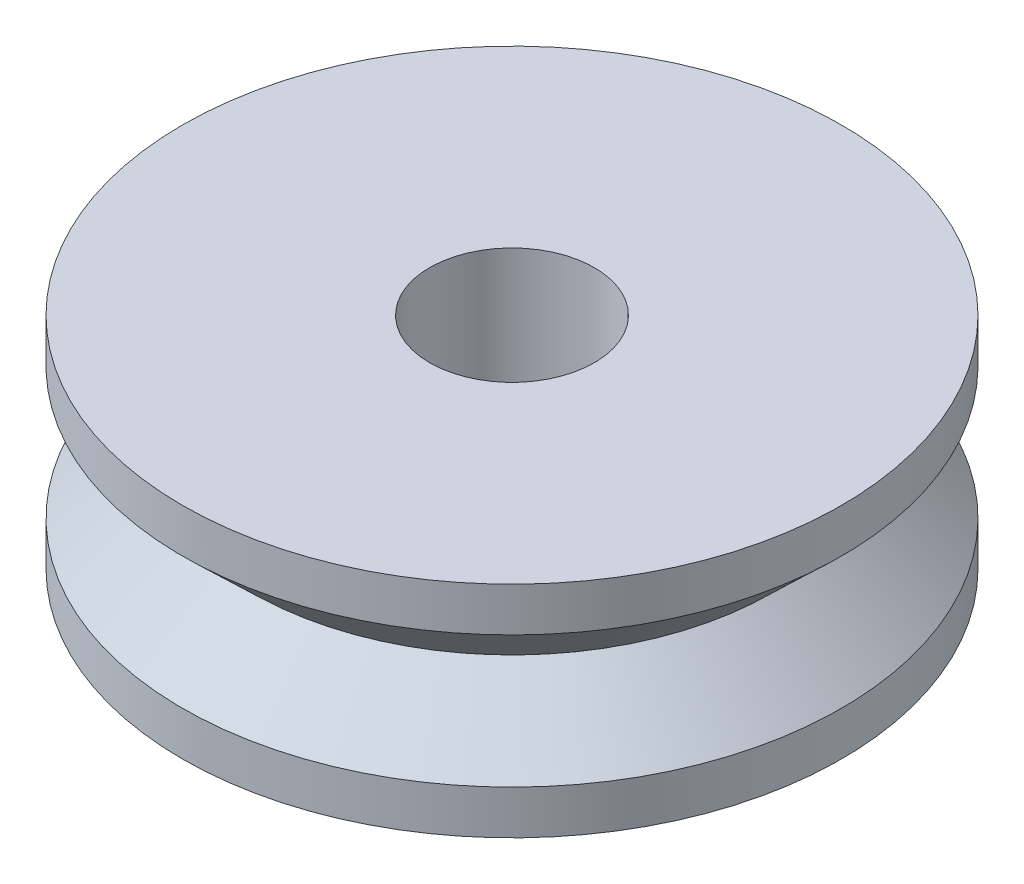
SolidWorks part; units mm, degrees
material "Plain Carbon Steel"
ref_plane "Front Plane" through (0, 0, 0) normal (0, 0, 1) x (1, 0, 0)
ref_plane "Top Plane" through (0, 0, 0) normal (0, 1, 0) x (1, 0, 0)
ref_plane "Right Plane" through (0, 0, 0) normal (1, 0, 0) x (0, 0, -1)
sketch "Sketch1" plane through (0, 0, 0) normal (0, 1, 0) x (1, 0, 0)
  circle A0 centre (0, 0) radius 1.5
  circle A1 centre (0, 0) radius 6
extrude "Boss-Extrude1" add sketch "Sketch1" along normal blind 4
sketch "Sketch2" plane through (0, 0, 0) normal (0, 0, 1) x (1, 0, 0)
  line L0 (-6, 3.2) -> (-6, 0.8)
  line L1 (-6, 4) -> (-6, 0) construction
  line L6 (-6, 3.2) -> (-4.75, 2)
  line L7 (-4.75, 2) -> (-6, 0.8)
  point P8 (0, 0)
ref_plane "Plane1" through (0, 2, 0) normal (0, 1, 0) x (1, 0, 0)
sketch "Sketch3" plane through (0, 2, 0) normal (0, 1, 0) x (1, 0, 0)
  circle A0 centre (0, 0) radius 6
sweep "Cut-Sweep3" cut profiles "Sketch2" path "Sketch3"
